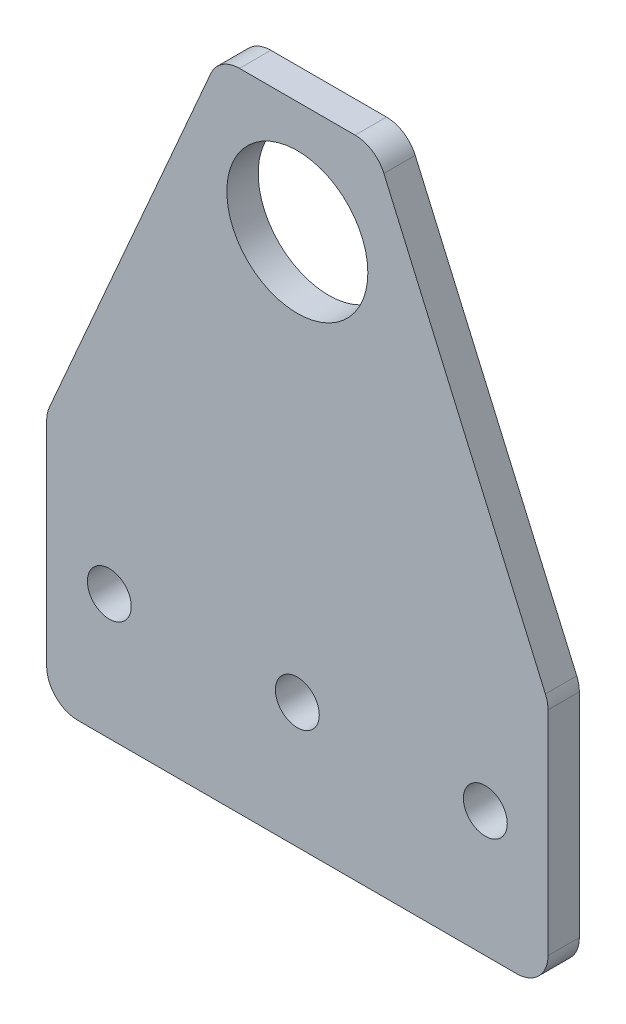
SolidWorks part; units mm, degrees
ref_plane "Plan de face" through (0, 0, 0) normal (0, 0, 1) x (1, 0, 0)
ref_plane "Plan de dessus" through (0, 0, 0) normal (0, 1, 0) x (1, 0, 0)
ref_plane "Plan de droite" through (0, 0, 0) normal (1, 0, 0) x (0, 0, -1)
sketch "Esquisse1" plane through (0, 0, 0) normal (0, 0, 1) x (1, 0, 0)
  line L0 (0, 0) -> (0, 103) construction
  line L1 (-40, 0) -> (40, 0)
  line L2 (40, 0) -> (40, 40)
  line L3 (40, 40) -> (12.5, 103)
  line L4 (12.5, 103) -> (-12.5, 103)
  line L5 (-40, 40) -> (-12.5, 103)
  line L6 (-40, 0) -> (-40, 40)
  line L7 (-40, 20) -> (40, 20) construction
  circle A0 centre (0, 85) radius 11.25
  circle A1 centre (0, 20) radius 3.5
  circle A2 centre (30, 20) radius 3.5
  circle A3 centre (-30, 20) radius 3.5
  dimension "D5" = 22.5
  dimension "D6" = 18
  dimension "D8" = 7
  dimension "D9" = 30
  dimension "D1" = 80
  dimension "D2" = 40
  dimension "D3" = 25
  dimension "D4" = 45
  dimension "D7" = 20
extrude "Boss.-Extru.1" add sketch "Esquisse1" along normal blind 5
fillet "Congé1" radius 5 6 edges at (12.5, 103, 2.5) (-12.5, 103, 2.5) (-40, 40, 2.5) (40, 40, 2.5) (40, 0, 2.5) (-40, 0, 2.5)
